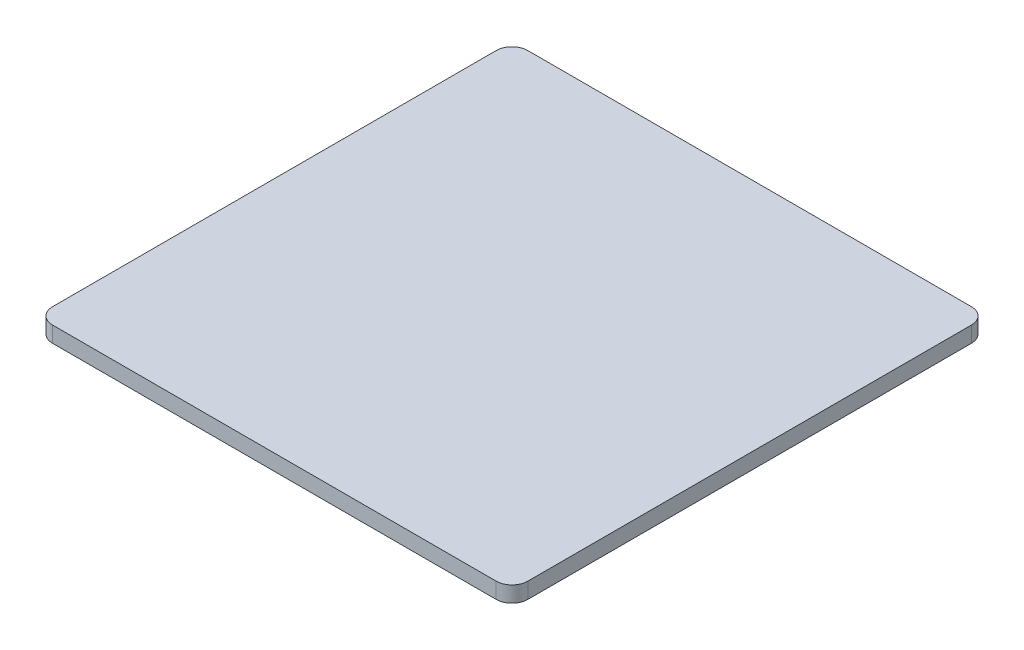
SolidWorks part; units mm, degrees
ref_plane "Front Plane" through (0, 0, 0) normal (0, 0, 1) x (1, 0, 0)
ref_plane "Top Plane" through (0, 0, 0) normal (0, 1, 0) x (1, 0, 0)
ref_plane "Right Plane" through (0, 0, 0) normal (1, 0, 0) x (0, 0, -1)
sketch "Sketch1" plane through (0, 0, 0) normal (0, 1, 0) x (1, 0, 0)
  line L1 (140, 150) -> (-140, 150)
  line L2 (150, 140) -> (150, -140)
  line L3 (140, -150) -> (-140, -150)
  line L4 (-150, 140) -> (-150, -140)
  line L5 (150, 150) -> (-150, -150) construction
  line L6 (150, -150) -> (-150, 150) construction
  arc A0 (-140, -150) -> (-150, -140) centre (-140, -140) cw
  arc A1 (150, -140) -> (140, -150) centre (140, -140) cw
  arc A2 (140, 150) -> (150, 140) centre (140, 140) cw
  arc A3 (-140, 150) -> (-150, 140) centre (-140, 140) ccw
  point P0 (0, 0)
  dimension "D3" = 10
  dimension "D1" = 300
  dimension "D2" = 300
extrude "Boss-Extrude1" add sketch "Sketch1" along normal blind 10
